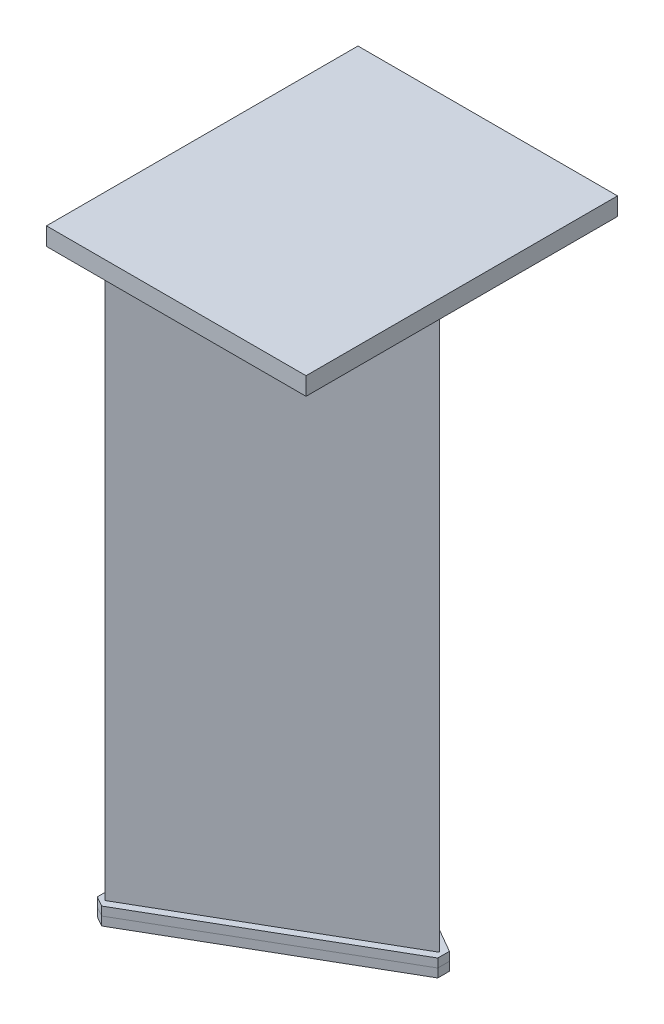
SolidWorks part; units mm, degrees
ref_plane "Front" through (0, 0, 0) normal (0, 0, 1) x (1, 0, 0)
ref_plane "Top" through (0, 0, 0) normal (0, 1, 0) x (1, 0, 0)
ref_plane "Right" through (0, 0, 0) normal (1, 0, 0) x (0, 0, -1)
sketch "Sketch31" plane through (0, 0, 0) normal (0, 1, 0) x (1, 0, 0)
  line L0 (-228.2613, 361.2226) -> (-228.2613, -361.2226)
  line L1 (-198.6973, -378.2914) -> (426.9586, -17.0688)
  line L2 (426.9586, 17.0688) -> (-198.6973, 378.2914)
  line L3 (0, 0) -> (103.7167, 179.6425) construction
  line L4 (0, 0) -> (103.7167, -179.6425) construction
  line L5 (0, 0) -> (-207.4333, 0) construction
  line L6 (414.8667, 0) -> (-207.4333, 359.2851) construction
  line L7 (-419.1, 0) -> (419.1, 0) construction
  line L8 (-207.4333, -359.2851) -> (414.8667, 0) construction
  line L9 (-228.2613, 361.2226) -> (-198.6973, 378.2914)
  line L10 (426.9586, 17.0688) -> (426.9586, -17.0688)
  line L11 (-198.6973, -378.2914) -> (-228.2613, -361.2226)
  line L12 (-207.4333, 359.2851) -> (-207.4333, -359.2851) construction
  point P2 (0, 452.7127)
  point P4 (-392.0607, -226.3563)
  point P5 (392.0607, -226.3563)
  dimension "D3" = 34.1376
  dimension "D1" = 622.3
  dimension "D2" = 20.828
  dimension "D4" = 30
extrude "Base & Grout" add sketch "Sketch31" along normal blind 25.4 separate body
sketch "Sketch33" plane through (0, 0, 0) normal (0, 1, 0) x (1, 0, 0)
  line L0 (-281.6513, 457.2) -> (480.3487, -457.2) construction
  line L1 (-281.6513, -457.2) -> (480.3487, -457.2)
  line L2 (-281.6513, -457.2) -> (-281.6513, 457.2)
  line L3 (-281.6513, 457.2) -> (480.3487, 457.2)
  line L4 (480.3487, -457.2) -> (480.3487, 457.2)
  line L5 (426.9586, 17.0688) -> (480.3487, 17.0688) construction
  line L6 (-228.2613, 361.2226) -> (-281.6513, 361.2226) construction
  point P4 (99.3487, 0)
  dimension "D1" = 914.4
  dimension "D2" = 762
  dimension "D3" = 99.3487
extrude "Table" add sketch "Sketch33" against normal blind 52.451 from offset 1752.6 separate body
sketch "Sketch1" plane through (0, 25.4, -25.4) normal (0, -1, 0) x (1, 0, 0)
  line L0 (-228.2613, -335.8226) -> (-228.2613, 386.6226) construction
  line L1 (414.8667, 25.4) -> (-207.4333, 384.6851)
  line L2 (-207.4333, 384.6851) -> (-207.4333, -333.8851)
  line L3 (-207.4333, -333.8851) -> (414.8667, 25.4)
  circle A0 centre (0, 25.4) radius 207.4333 construction
  dimension "D1" = 622.3
extrude "Pier Body" add sketch "Sketch1" against normal up to surface (1674.749 mm away) separate body up to face at (99.3487, 1700.149, 0)
sketch "Sketch32" plane through (0, 0, 0) normal (0, -1, 0) x (-1, 0, 0)
  line L6 (228.2613, 361.2226) -> (198.6973, 378.2914)
  line L7 (228.2613, -361.2226) -> (228.2613, 361.2226)
  line L8 (198.6973, -378.2914) -> (228.2613, -361.2226)
  line L9 (-426.9586, -17.0688) -> (198.6973, -378.2914)
  line L10 (-426.9586, 17.0688) -> (-426.9586, -17.0688)
  line L11 (198.6973, 378.2914) -> (-426.9586, 17.0688)
  line L12 (228.2613, 361.2226) -> (198.6973, 378.2914)
  line L13 (228.2613, -361.2226) -> (228.2613, 361.2226)
  line L14 (198.6973, -378.2914) -> (228.2613, -361.2226)
  line L15 (-426.9586, -17.0688) -> (198.6973, -378.2914)
  line L16 (-426.9586, 17.0688) -> (-426.9586, -17.0688)
  line L17 (198.6973, 378.2914) -> (-426.9586, 17.0688)
  dimension "D1" = 0
extrude "LHO 1\" Lift" add sketch "Sketch32" along normal blind 25.4 separate body
ref_plane "Lateral Table Center" through (99.3487, 0, 0) normal (1, 0, 0) x (0, 0, -1)
sketch "Cover & VP Outline" plane through (99.3487, 0, 0) normal (1, 0, 0) x (0, 0, -1)
  line L0 (593.725, 1854.2) -> (593.725, 1717.675) construction
  line L1 (0, 419.1) -> (0, -419.1) construction
  line L2 (584.2, 1854.2) -> (584.2, 1749.05) construction
  line L4 (558.8, 1981.2) -> (558.8, 1727.2) construction
  line L6 (419.1, 0) -> (-419.1, 0) construction
  line L7 (495.935, 1990.725) -> (593.725, 1990.725) construction
  line L8 (495.935, 1990.725) -> (495.935, 1717.675) construction
  line L9 (495.935, 1717.675) -> (593.725, 1717.675) construction
  line L10 (593.725, 1990.725) -> (593.725, 1854.2) construction
  line L11 (558.8, 1981.2) -> (584.2, 1981.2) construction
  line L12 (534.162, 1981.2) -> (534.162, 1955.8) construction
  line L13 (558.8, 1727.2) -> (584.2, 1727.2) construction
  line L14 (584.2, 1959.35) -> (584.2, 1854.2) construction
  line L15 (584.2, 1959.35) -> (635, 1959.35) construction
  line L16 (584.2, 1749.05) -> (635, 1749.05) construction
  line L17 (584.2, 1959.35) -> (584.2, 1981.2) construction
  line L18 (584.2, 1749.05) -> (584.2, 1727.2) construction
  line L19 (534.162, 1955.8) -> (509.524, 1955.8) construction
  line L20 (509.524, 1955.8) -> (509.524, 1752.6) construction
  line L21 (509.524, 1752.6) -> (534.162, 1752.6) construction
  line L22 (558.8, 1727.2) -> (534.162, 1727.2) construction
  line L23 (558.8, 1981.2) -> (534.162, 1981.2) construction
  line L24 (534.162, 1752.6) -> (534.162, 1727.2) construction
  line L25 (534.162, 1955.8) -> (534.162, 1752.6) construction
  point P3 (553.8, 1854.2)
  dimension "D2" = 584.2
  dimension "D3" = 5
  dimension "D4" = 97.79
  dimension "D6" = 1854.2
  dimension "D7" = 254
  dimension "D8" = 50.038
  dimension "D9" = 9.525
  dimension "D10" = 38.227
  dimension "D11" = 273.05
  dimension "D12" = 25.4
  dimension "D13" = 210.3
  dimension "D14" = 50.8
  dimension "D15" = 203.2
ref_plane "Beam Transmission Plane" through (0, 0, -441.325) normal (0, 0, 1) x (1, 0, 0)
ref_plane "\"Beam Entry\" Plane" through (0, 0, -553.8) normal (0, 0, 1) x (1, 0, 0)
sketch3d "3DSketch ETM-Y  BSC6-H2"
  line L0 (306.0072, 1861.3504, -441.325) -> (318.3605, 1858.8079, -481.3187)
  line L1 (306.0072, 1861.3504, -441.325) -> (318.3605, 1861.3504, -481.3187) construction
  line L2 (306.0072, 1861.3504, -441.325) -> (306.0072, 1861.3504, -481.3187) construction
  line L3 (416.7487, 1854.2, -553.8) -> (340.7487, 1854.2, -553.8) construction
  line L4 (379.1479, 1853.0098, -441.325) -> (379.1479, 1853.0098, -481.7247) construction
  line L5 (379.1479, 1853.0098, -441.325) -> (392.6536, 1853.0098, -481.7247) construction
  line L6 (416.7487, 1854.2, -553.8) -> (392.6536, 1853.4373, -481.7247)
  line L7 (318.3605, 1858.8079, -481.3187) -> (340.7487, 1854.2, -553.8)
  line L8 (392.6536, 1853.4373, -481.7247) -> (379.1479, 1853.0098, -441.325)
  point P7 (378.7487, 1854.2, -553.8)
  dimension "D1" = 17.165
  dimension "D2" = 17.503
  dimension "D4" = 76
  dimension "D6" = 18.485
  dimension "D7" = 18.494
  dimension "Lateral Launch Position" = 279.4
ref_plane "AdvLIGO Front Plane BSC6-H2" through (0, 0, -553.8) normal (0, 0, 1) x (1, 0, 0)
ref_plane "AdvLIGO Top Plane BSC6-H2" through (0, 1854.2, 0) normal (0, 1, 0) x (-1, 0, 0)
ref_plane "AdvLIGO Right Plane BSC6-H2" through (378.7487, 0, 0) normal (1, 0, 0) x (0, 0, -1)
sketch "BSC6-H2 ETM-Y Axial" plane through (-33.0069, 0, -562.69) normal (0, 0, 1) x (1, 0, 0)
  circle B0 centre (1099.8069, 1854.2) radius 762 construction
  circle B1 centre (1299.8069, 1774.2) radius 170
  circle B2 centre (1245.2033, 1106.2001) radius 68.326
  circle B3 centre (954.4104, 1106.2001) radius 68.326
  circle B4 centre (1666.0832, 2364.0775) radius 98.806
  circle B5 centre (533.5305, 2364.0775) radius 98.806
  circle B6 centre (1861.8069, 1854.2) radius 68.326
  circle B7 centre (337.8069, 1854.2) radius 68.326
  circle B8 centre (899.8069, 1774.2) radius 170
  line B9 (1099.8069, 1854.2) -> (1099.8069, 1092.2) construction
  circle B10 centre (337.8069, 1854.2) radius 98.806
  circle B11 centre (1861.8069, 1854.2) radius 98.806
sketch_block_instance "Block-TM Axial-1"
sketch_block "Block-TM Axial" parameters "D1"=340, "D4"=1524, "D5"=136.652, "D7"=136.652, "D8"=1160.6109, "D9"=2311.0519, "D2"=200, "D3"=80, "D6"=400
sketch3d "3DSketch ETM-X BSC5-H2" [suppressed]
  line L0 (-379.4314, 1853.0107, -441.325) -> (-379.4314, 1853.0107, -481.6702) construction
  line L1 (-379.4314, 1853.0107, -441.325) -> (-392.8172, 1853.0107, -481.6702) construction
  line L2 (-379.4314, 1853.0107, -441.325) -> (-392.8172, 1853.4373, -481.6702)
  line L3 (-416.7487, 1854.2, -553.8) -> (-340.7487, 1854.2, -553.8) construction
  line L4 (-306.2651, 1861.3458, -441.325) -> (-306.2651, 1861.3458, -481.272) construction
  line L5 (-306.2651, 1861.3458, -441.325) -> (-318.5124, 1861.3458, -481.272) construction
  line L6 (-306.2651, 1861.3458, -441.325) -> (-318.5124, 1858.8079, -481.272)
  line L7 (-392.8172, 1853.4373, -481.6702) -> (-416.7487, 1854.2, -553.8)
  line L8 (-318.5124, 1858.8079, -481.272) -> (-340.7487, 1854.2, -553.8)
  point P6 (-378.7487, 1854.2, -553.8)
  dimension "D1" = 18.355
  dimension "D4" = 76
  dimension "D2" = 18.364
  dimension "D6" = 17.045
  dimension "D7" = 17.385
ref_plane "AdvLIGO Front Plane BSC5-H2" [suppressed] through (0, 0, -553.8) normal (0, 0, 1) x (1, 0, 0)
ref_plane "AdvLIGO Top Plane BSC5-H2" [suppressed] through (0, 1854.2, 0) normal (0, 1, 0) x (-1, 0, 0)
ref_plane "AdvLIGO Right Plane BSC5-H2" [suppressed] through (-378.7487, 0, 0) normal (1, 0, 0) x (0, 0, -1)
sketch "BSC5-H2 ETM-X Axial" plane through (0, 0, -562.69) normal (0, 0, -1) x (-1, 0, 0)
  circle B0 centre (1066.8, 1854.2) radius 762 construction
  circle B1 centre (1266.8, 1774.2) radius 170
  circle B2 centre (1212.1965, 1106.2001) radius 68.326
  circle B3 centre (921.4035, 1106.2001) radius 68.326
  circle B4 centre (1633.0764, 2364.0775) radius 98.806
  circle B5 centre (500.5236, 2364.0775) radius 98.806
  circle B6 centre (1828.8, 1854.2) radius 68.326
  circle B7 centre (304.8, 1854.2) radius 68.326
  circle B8 centre (866.8, 1774.2) radius 170
  line B9 (1066.8, 1854.2) -> (1066.8, 1092.2) construction
  circle B10 centre (304.8, 1854.2) radius 98.806
  circle B11 centre (1828.8, 1854.2) radius 98.806
  circle B12 centre (1066.8, 1854.2) radius 568.325 construction
  circle B13 centre (1066.8, 1854.2) radius 612.521 construction
sketch_block_instance "Block-TM Axial-7"
sketch3d "3DSketch ETM-X  BSC9-H1 BSC4-L1" [suppressed]
  line L0 (319.8983, 1858.2477, -441.325) -> (326.5165, 1856.8921, -478.9935)
  line L1 (319.8983, 1858.2477, -441.325) -> (326.5165, 1858.2477, -478.9935) construction
  line L2 (319.8983, 1858.2477, -441.325) -> (319.8983, 1858.2477, -478.9935) construction
  line L3 (415.6598, 1854.2, -553.8) -> (339.6598, 1854.2, -553.8) construction
  line L4 (394.2753, 1853.5406, -479.1387) -> (394.2753, 1853.5406, -441.325) construction
  line L5 (394.2753, 1853.5406, -441.325) -> (401.4647, 1853.5406, -479.1387) construction
  line L6 (394.2753, 1853.5406, -441.325) -> (401.4647, 1853.7623, -479.1387)
  line L7 (326.5165, 1856.8921, -478.9935) -> (339.6598, 1854.2, -553.8)
  line L8 (401.4647, 1853.7623, -479.1387) -> (415.6598, 1854.2, -553.8)
  point P5 (377.6598, 1854.2, -553.8)
  dimension "D3" = 10.168
  dimension "D2" = 9.965
  dimension "D6" = 10.765
  dimension "D5" = 76
  dimension "D7" = 10.77
ref_plane "AdvLIGO Front Plane BSC9-H1 BSC4-L1" [suppressed] through (0, 0, -553.8) normal (0, 0, 1) x (1, 0, 0)
ref_plane "AdvLIGO Top Plane BSC9-H1 BSC4-L1" [suppressed] through (0, 1854.2, 0) normal (0, 1, 0) x (-1, 0, 0)
ref_plane "AdvLIGO Right Plane BSC9-H1 BSC4-L1" [suppressed] through (377.6598, 0, 0) normal (1, 0, 0) x (0, 0, -1)
sketch "BSC9-H1 BSC4-L1 ETM-X Axial" plane through (0, 0, -562.69) normal (0, 0, 1) x (1, 0, 0)
  circle B0 centre (1066.8, 1854.2) radius 762 construction
  circle B1 centre (1266.8, 1774.2) radius 170
  circle B2 centre (1212.1965, 1106.2001) radius 68.326
  circle B3 centre (921.4035, 1106.2001) radius 68.326
  circle B4 centre (1633.0764, 2364.0775) radius 98.806
  circle B5 centre (500.5236, 2364.0775) radius 98.806
  circle B6 centre (1828.8, 1854.2) radius 68.326
  circle B7 centre (304.8, 1854.2) radius 68.326
  circle B8 centre (866.8, 1774.2) radius 170
  line B9 (1066.8, 1854.2) -> (1066.8, 1092.2) construction
  circle B10 centre (304.8, 1854.2) radius 98.806
  circle B11 centre (1828.8, 1854.2) radius 98.806
  circle B12 centre (1066.8, 1854.2) radius 568.325 construction
  circle B13 centre (1066.8, 1854.2) radius 612.521 construction
sketch_block_instance "Block-TM Axial-6"
sketch3d "3DSketch ETM-Y BSC10-H1 BSC5-L1" [suppressed]
  line L0 (-394.2752, 1853.5404, -441.325) -> (-394.2752, 1853.5404, -479.1387) construction
  line L1 (-394.2752, 1853.5404, -441.325) -> (-401.4647, 1853.5404, -479.1387) construction
  line L2 (-394.2752, 1853.5404, -441.325) -> (-401.4647, 1853.7622, -479.1387)
  line L3 (-339.6598, 1854.2, -553.8) -> (-415.6598, 1854.2, -553.8) construction
  line L4 (-319.8983, 1858.2477, -441.325) -> (-319.8983, 1858.2477, -478.9935) construction
  line L5 (-319.8983, 1858.2477, -441.325) -> (-326.5165, 1858.2477, -478.9935) construction
  line L6 (-319.8983, 1858.2477, -441.325) -> (-326.5165, 1856.8921, -478.9935)
  line L7 (-401.4647, 1853.7622, -479.1387) -> (-415.6598, 1854.2, -553.8)
  line L8 (-326.5165, 1856.8921, -478.9935) -> (-339.6598, 1854.2, -553.8)
  point P4 (-377.6598, 1854.2, -553.8)
  dimension "D2" = 10.765
  dimension "D3" = 10.77
  dimension "D6" = 9.965
  dimension "D4" = 76
  dimension "D7" = 10.168
ref_plane "AdvLIGO Front Plane BSC10-H1 BSC5-L1" [suppressed] through (0, 0, -553.8) normal (0, 0, 1) x (1, 0, 0)
ref_plane "AdvLIGO Top Plane BSC10-H1 BSC5-L1" [suppressed] through (0, 1854.2, 0) normal (0, 1, 0) x (-1, 0, 0)
ref_plane "AdvLIGO Right Plane BSC10-H1 BSC5-L1" [suppressed] through (-377.6598, 0, 0) normal (1, 0, 0) x (0, 0, -1)
sketch "BSC10-H1 BSC5-L1 ETM-Y Axial" plane through (0, 0, -562.69) normal (0, 0, 1) x (1, 0, 0)
  circle B0 centre (-893.2927, 1854.2) radius 762 construction
  circle B1 centre (-693.2927, 1774.2) radius 170
  circle B2 centre (-747.8962, 1106.2001) radius 68.326
  circle B3 centre (-1038.6892, 1106.2001) radius 68.326
  circle B4 centre (-327.0163, 2364.0775) radius 98.806
  circle B5 centre (-1459.5691, 2364.0775) radius 98.806
  circle B6 centre (-131.2927, 1854.2) radius 68.326
  circle B7 centre (-1655.2927, 1854.2) radius 68.326
  circle B8 centre (-1093.2927, 1774.2) radius 170
  line B9 (-893.2927, 1854.2) -> (-893.2927, 1092.2) construction
  circle B10 centre (-1655.2927, 1854.2) radius 98.806
  circle B11 centre (-131.2927, 1854.2) radius 98.806
  circle B12 centre (-893.2927, 1854.2) radius 568.325 construction
  circle B13 centre (-893.2927, 1854.2) radius 612.521 construction
sketch_block_instance "Block-TM Axial-8"
